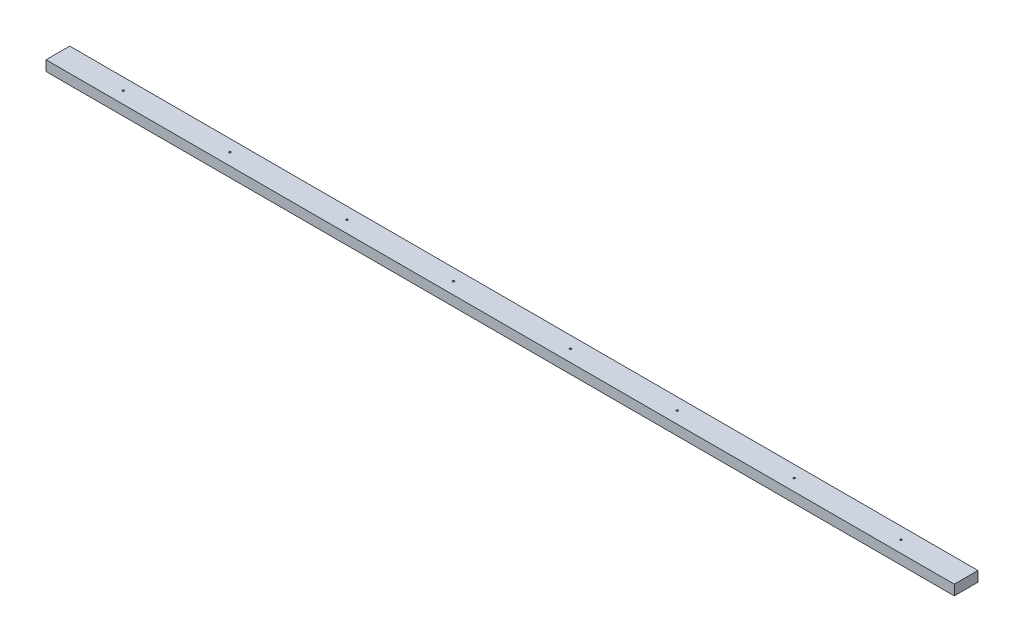
SolidWorks part; units mm, degrees
ref_plane "Front Plane" through (0, 0, 0) normal (0, 0, 1) x (1, 0, 0)
ref_plane "Top Plane" through (0, 0, 0) normal (0, 1, 0) x (1, 0, 0)
ref_plane "Right Plane" through (0, 0, 0) normal (1, 0, 0) x (0, 0, -1)
sketch "Sketch1" plane through (0, 0, 0) normal (1, 0, 0) x (0, 0, -1)
  line L1 (-44.45, -19.05) -> (44.45, -19.05)
  line L2 (-44.45, -19.05) -> (-44.45, 19.05)
  line L3 (-44.45, 19.05) -> (44.45, 19.05)
  line L4 (44.45, -19.05) -> (44.45, 19.05)
  line L5 (-44.45, -19.05) -> (44.45, 19.05) construction
  line L6 (-44.45, 19.05) -> (44.45, -19.05) construction
  point P0 (0, 0)
  dimension "D1" = 88.9
  dimension "D2" = 38.1
extrude "Boss-Extrude1" add sketch "Sketch1" along normal blind 3403.6
sketch "Sketch2" plane through (0, -19.05, 0) normal (0, -1, 0) x (1, 0, 0)
  circle A0 centre (244.529, 0) radius 3.5815
  circle A1 centre (644.529, 0) radius 3.5815
  circle A2 centre (1082.729, 0) radius 3.5815
  circle A3 centre (1482.729, 0) radius 3.5815
  circle A4 centre (1920.929, 0) radius 3.5815
  circle A5 centre (2320.929, 0) radius 3.5815
  circle A6 centre (2759.129, 0) radius 3.5815
  circle A7 centre (3159.129, 0) radius 3.5815
  point P24 (0, 0)
  dimension "D1" = 7.163
extrude "Cut-Extrude1" cut sketch "Sketch2" against normal through all
